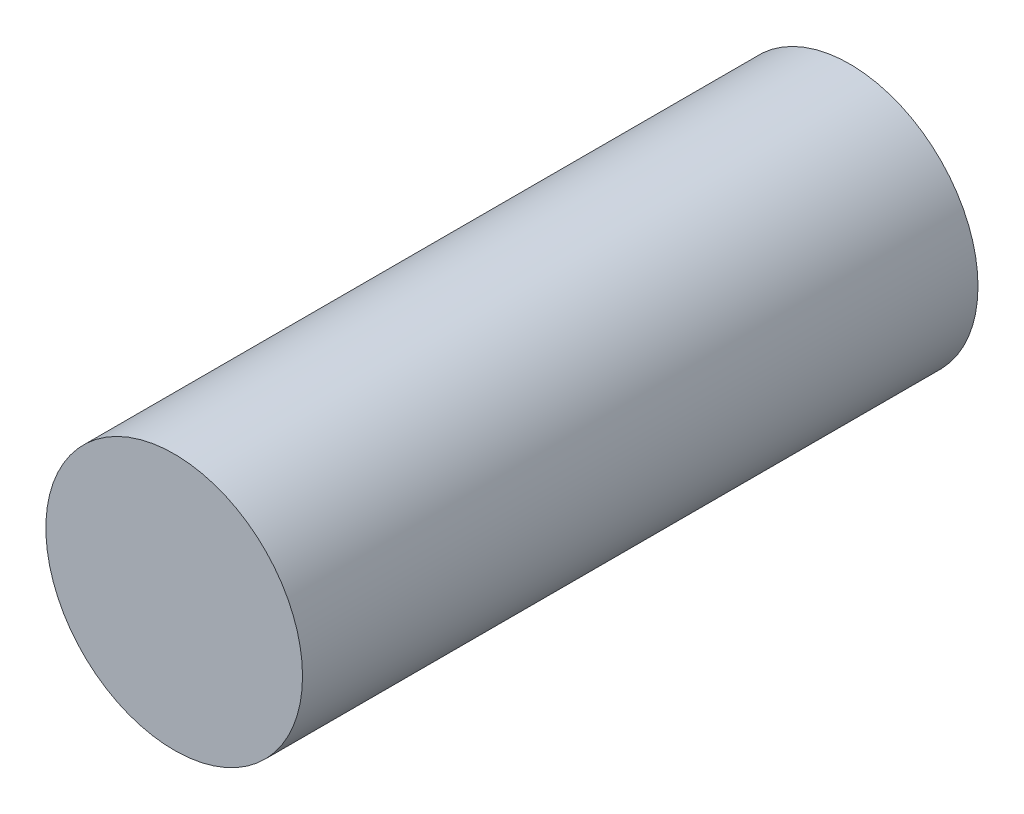
SolidWorks part; units mm, degrees
ref_plane "Front Plane" through (0, 0, 0) normal (0, 0, 1) x (1, 0, 0)
ref_plane "Top Plane" through (0, 0, 0) normal (0, 1, 0) x (1, 0, 0)
ref_plane "Right Plane" through (0, 0, 0) normal (1, 0, 0) x (0, 0, -1)
sketch "Sketch1" plane through (0, 0, 0) normal (0, 0, 1) x (1, 0, 0)
  circle A0 centre (0, 0) radius 4.75
  dimension "D1" = 9.5
extrude "Boss-Extrude1" add sketch "Sketch1" along normal blind 25
